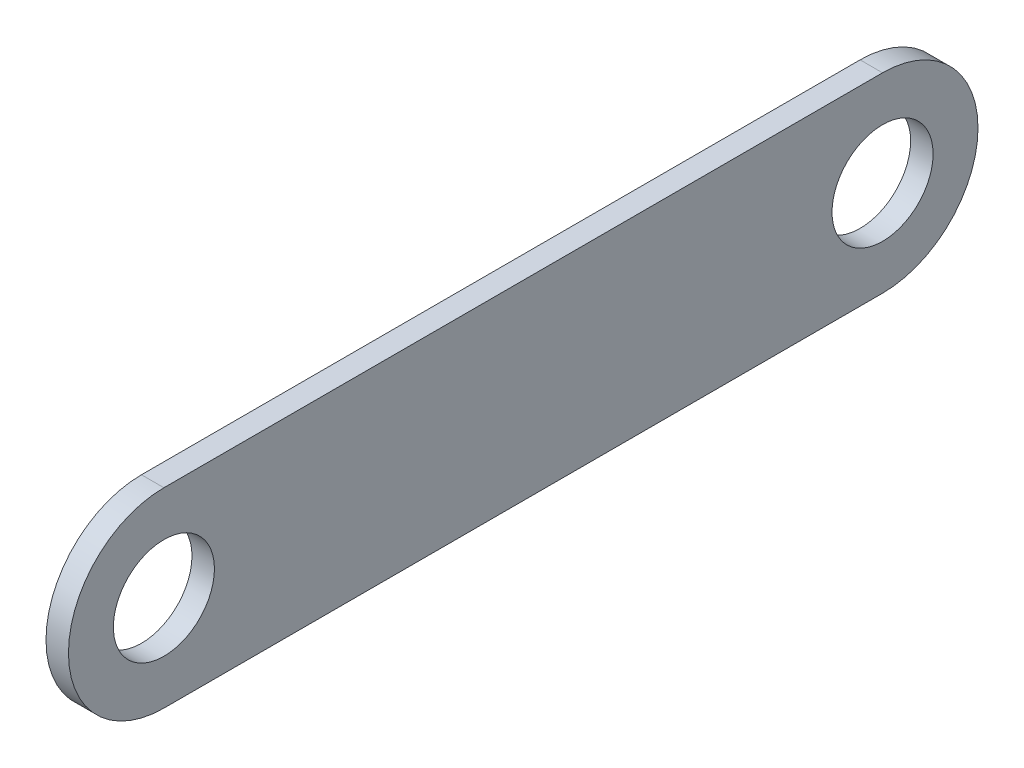
SolidWorks part; units mm, degrees
material "PC High Viscosity"
ref_plane "Front Plane" through (0, 0, 0) normal (0, 0, 1) x (1, 0, 0)
ref_plane "Top Plane" through (0, 0, 0) normal (0, 1, 0) x (1, 0, 0)
ref_plane "Right Plane" through (0, 0, 0) normal (1, 0, 0) x (0, 0, -1)
sketch "Sketch1" plane through (0, 0, 0) normal (1, 0, 0) x (0, 0, -1)
  line L0 (0, 26.9875) -> (203.2, 26.9875)
  line L1 (0, -26.9875) -> (203.2, -26.9875)
  line L2 (203.2, -26.9875) -> (203.2, 26.9875) construction
  line L3 (0, -26.9875) -> (203.2, 26.9875) construction
  line L4 (9.6255, 20.6375) -> (36.0341, -10.8457) construction
  line L5 (36.0341, -10.8457) -> (154.5592, 20.6375) construction
  line L6 (154.5592, 20.6375) -> (9.6255, 20.6375) construction
  line L7 (0, 26.9875) -> (203.2, -26.9875) construction
  line L8 (101.6, 0) -> (101.6, -26.9875) construction
  line L12 (101.6, 0) -> (-26.9875, 0) construction
  line L13 (166.4488, -20.6375) -> (146.4874, 10.8457) construction
  line L14 (42.7779, -20.6375) -> (166.4488, -20.6375) construction
  line L15 (146.4874, 10.8457) -> (42.7779, -20.6375) construction
  circle A0 centre (0, 0) radius 14.2875
  arc A1 (0, 26.9875) -> (0, -26.9875) centre (0, 0) ccw
  arc A2 (203.2, -26.9875) -> (203.2, 26.9875) centre (203.2, 0) ccw
  circle A3 centre (203.2, 0) radius 14.2875
  dimension "D1" = 28.575
  dimension "D2" = 12.7
  dimension "D5" = 28.575
  dimension "D3" = 203.2
  dimension "D4" = 203.2
  dimension "D6" = 6.35
  dimension "D7" = 6.35
  dimension "D8" = 20.6375
  dimension "D9" = 10.8457
extrude "Boss-Extrude1" add sketch "Sketch1" along normal blind 6.35 contours L1 A2 L0 A1 A3 L6 L5 L4 L15 L13 L14 A0
